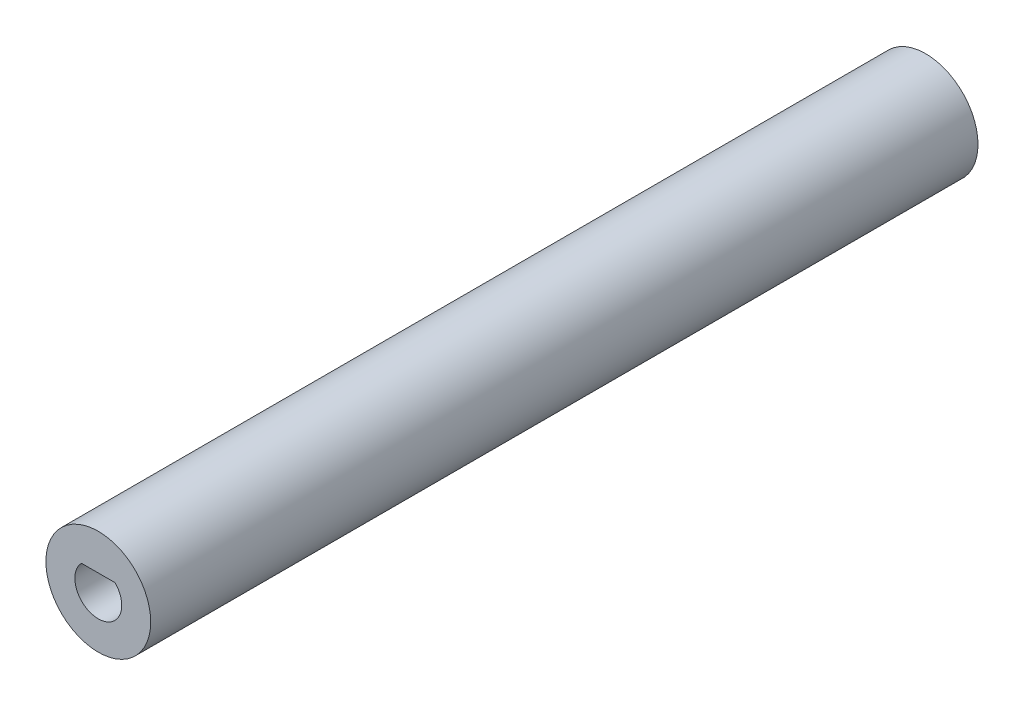
SolidWorks part; units mm, degrees
ref_plane "Front Plane" through (0, 0, 0) normal (0, 0, 1) x (1, 0, 0)
ref_plane "Top Plane" through (0, 0, 0) normal (0, 1, 0) x (1, 0, 0)
ref_plane "Right Plane" through (0, 0, 0) normal (1, 0, 0) x (0, 0, -1)
sketch "Sketch1" plane through (0, 0, 0) normal (0, 0, 1) x (1, 0, 0)
  circle A0 centre (0, 0) radius 4.75
  dimension "D1" = 9.5
extrude "Boss-Extrude1" add sketch "Sketch1" along normal blind 75
sketch "Sketch2" plane through (0, 0, 75) normal (0, 0, 1) x (1, 0, 0)
  line L0 (-1.5297, 1.475) -> (1.5297, 1.475)
  line L1 (0, 1.475) -> (0, -2.125) construction
  arc A0 (-1.5297, 1.475) -> (1.5297, 1.475) centre (0, 0) ccw
  arc A1 (1.5297, 1.475) -> (-1.5297, 1.475) centre (0, 0) ccw construction
  dimension "D1" = 4.25
  dimension "D2" = 3.6
extrude "Cut-Extrude1" cut sketch "Sketch2" against normal blind 10
